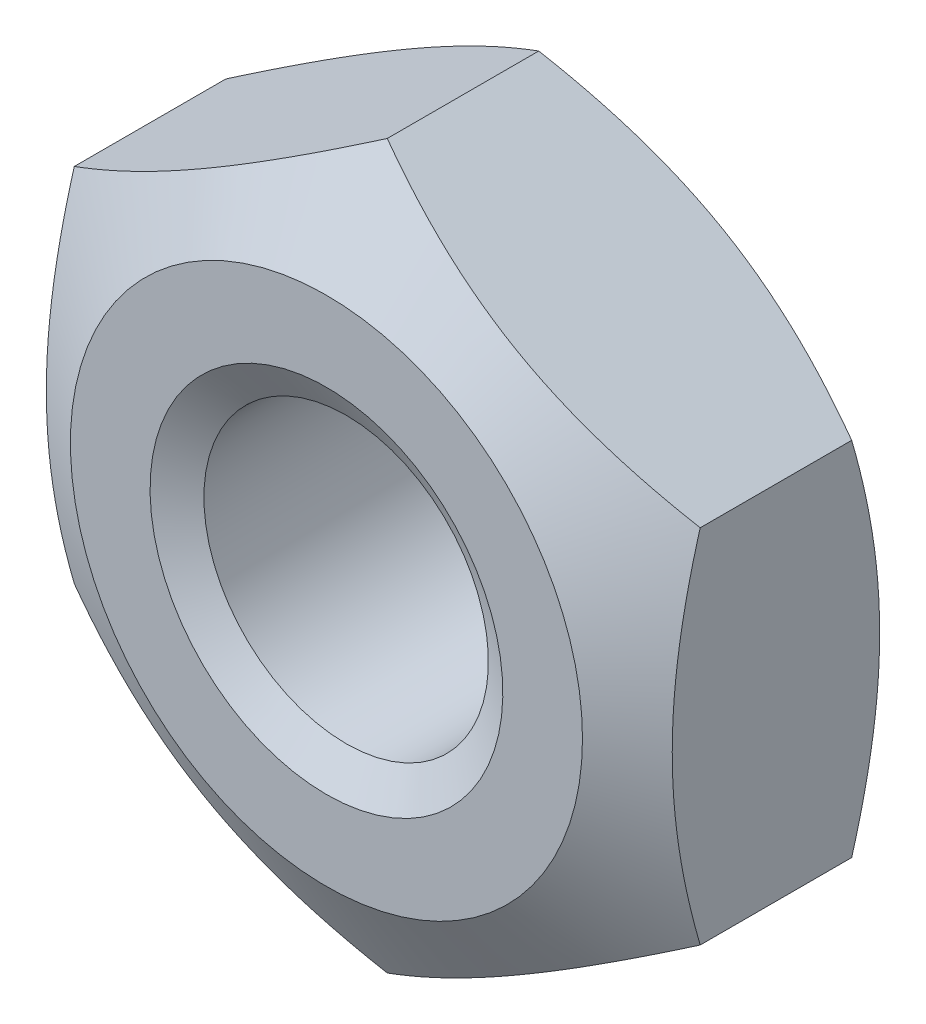
SolidWorks part; units mm, degrees
ref_plane "Front Plane" through (0, 0, 0) normal (0, 0, 1) x (1, 0, 0)
ref_plane "Top Plane" through (0, 0, 0) normal (0, 1, 0) x (1, 0, 0)
ref_plane "Right Plane" through (0, 0, 0) normal (1, 0, 0) x (0, 0, -1)
sketch "Sketch1" plane through (0, 0, 0) normal (0, 0, 1) x (1, 0, 0)
  line L0 (0, 0) -> (0, 3.1754) construction
  line L1 (0, 3.1754) -> (-2.75, 1.5877)
  line L2 (-2.75, 1.5877) -> (-2.75, -1.5877)
  line L3 (-2.75, -1.5877) -> (0, -3.1754)
  line L4 (0, -3.1754) -> (2.75, -1.5877)
  line L5 (2.75, -1.5877) -> (2.75, 1.5877)
  line L6 (2.75, 1.5877) -> (0, 3.1754)
  circle A0 centre (0, 0) radius 2.75 construction
  dimension "S DIM" = 5.5
extrude "Boss-Extrude1" add sketch "Sketch1" against normal blind 2.4
sketch "Sketch4" plane through (0, 0, 0) normal (1, 0, 0) x (0, 0, -1)
  line L0 (2.4, 3.1754) -> (1.8657, 3.1754)
  line L1 (2.4, 3.1754) -> (0, 3.1754) construction
  line L2 (1.8657, 3.1754) -> (2.4, 2.25)
  line L4 (2.4, 2.25) -> (2.4, 3.1754)
  line L5 (0, 0) -> (3.2979, 0) construction
  line L6 (0, 3.1754) -> (0.5343, 3.1754)
  line L7 (0.5343, 3.1754) -> (0, 2.25)
  line L9 (0, 2.25) -> (0, 3.1754)
  dimension "SAME S 1" = 4.5
  dimension "D2" = 30
  dimension "SAME S 2" = 4.5
  dimension "D4" = 30
revolve "Cut-Revolve1" cut sketch "Sketch4" angle 360 about L5
sketch "Sketch5" plane through (0, 0, 0) normal (1, 0, 0) x (0, 0, -1)
  line L0 (0, 0) -> (2.4, 0) construction
  line L1 (0, 0) -> (0, 1.55)
  line L2 (0, 2.25) -> (0, -2.25) construction
  line L3 (0, 1.55) -> (0.1732, 1.25)
  line L4 (0.1732, 1.25) -> (2.2268, 1.25)
  line L5 (2.2268, 1.25) -> (2.4, 1.55)
  line L6 (2.4, 1.55) -> (2.4, 0)
  line L8 (2.4, -2.25) -> (2.4, 2.25) construction
  line L9 (2.4, 0) -> (0, 0)
  dimension "D1" = 60
  dimension "D2" = 60
  dimension "Hole2" = 3.1
  dimension "Hole1" = 2.5
revolve "Cut-Revolve2" cut sketch "Sketch5" angle 360 about L0
